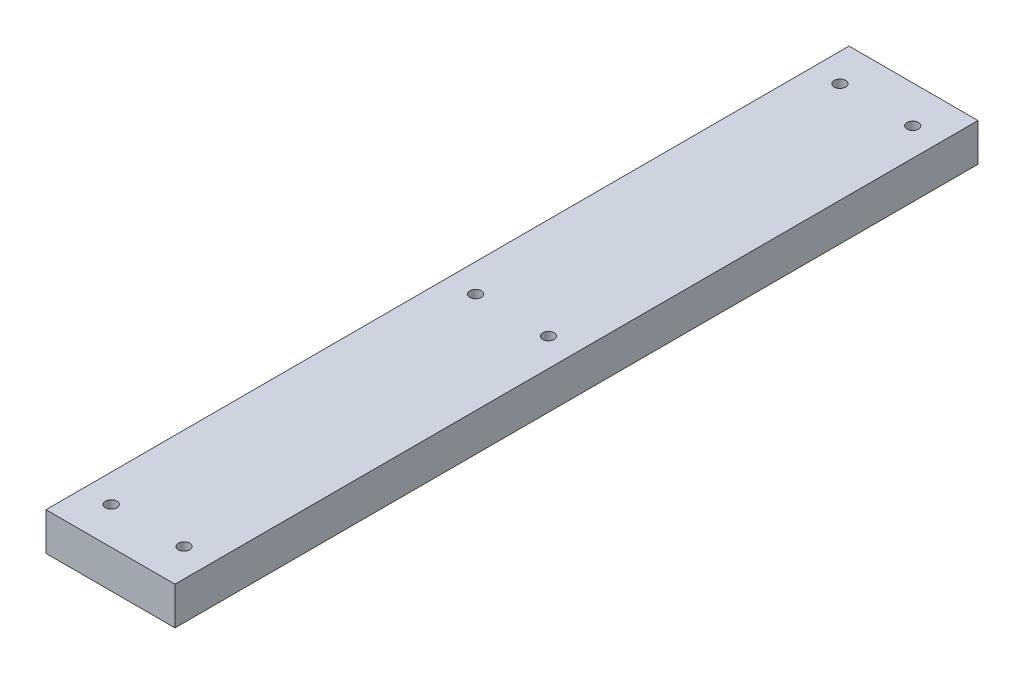
SolidWorks part; units mm, degrees
material "Acrylic (BLUE)"
ref_plane "Front Plane" through (0, 0, 0) normal (0, 0, 1) x (1, 0, 0)
ref_plane "Top Plane" through (0, 0, 0) normal (0, 1, 0) x (1, 0, 0)
ref_plane "Right Plane" through (0, 0, 0) normal (1, 0, 0) x (0, 0, -1)
sketch "Sketch1" plane through (0, 0, 0) normal (0, 1, 0) x (1, 0, 0)
  line L0 (-11.1125, 69.85) -> (11.1125, -69.85) construction
  line L1 (-11.1125, 69.85) -> (11.1125, 69.85)
  line L2 (-11.1125, 69.85) -> (-11.1125, -69.85)
  line L3 (-11.1125, -69.85) -> (11.1125, -69.85)
  line L4 (11.1125, 69.85) -> (11.1125, -69.85)
  line L5 (11.1125, -69.85) -> (10.7666, -69.6771) construction
  dimension "D1" = 139.7
  dimension "D2" = 22.225
extrude "Boss-Extrude1" add sketch "Sketch1" along normal blind 6.604
hole_wizard "#4-40 Tapped Hole1" positions "Sketch3" profile "Sketch4" tap size "#4-40" standard "ANSI Inch"
sketch "Sketch3" plane through (0, 6.604, 0) normal (0, 1, 0) x (1, 0, 0)
  line L0 (6.35, 69.85) -> (6.35, 63.5) construction
  line L1 (11.1125, 69.85) -> (-11.1125, 69.85) construction
  line L2 (6.35, 63.5) -> (6.35, 0) construction
  line L3 (6.35, 0) -> (6.35, -63.5) construction
  line L4 (6.35, -63.5) -> (6.35, -69.85) construction
  line L5 (-11.1125, -69.85) -> (11.1125, -69.85) construction
  line L7 (-6.35, 69.85) -> (-6.35, 63.5) construction
  line L8 (-6.35, 63.5) -> (-6.35, 0) construction
  line L9 (-6.35, 0) -> (-6.35, -63.5) construction
  line L10 (-6.35, -63.5) -> (-6.35, -69.85) construction
  line L12 (-6.35, 63.5) -> (-11.1125, 63.5) construction
  line L13 (-11.1125, 69.85) -> (-11.1125, -69.85) construction
  line L15 (6.35, 63.5) -> (11.1125, 63.5) construction
  line L16 (11.1125, -69.85) -> (11.1125, 69.85) construction
  point P1 (6.35, 63.5)
  point P5 (6.35, 0)
  point P7 (6.35, -63.5)
  point P14 (-6.35, 63.5)
  point P16 (-6.35, 0)
  point P18 (-6.35, -63.5)
  dimension "D1" = 12.7
  dimension "D2" = 63.5
sketch "Sketch4" plane through (6.35, 6.604, -63.5) normal (1, 0, 0) x (0, 0, 1)
  line L0 (0, 0) -> (0, 8.2738)
  line L1 (0, 8.2738) -> (1.1303, 7.5946)
  line L2 (1.1303, 7.5946) -> (1.1303, 0)
  line L5 (1.1303, 0) -> (0, 0)
  line L10 (0, 8.2738) -> (-1.1303, 7.5946) construction
  line L11 (0, -6.35) -> (0, 107.95) construction
  dimension "Tap Drill Dia." = 2.2606
  dimension "Tap Drill Depth" = 7.5946
  dimension "Drill Angle" = 118
other "Move Face1" face at (0, 3.302, 69.85) face at (6.35, 6.604, 1.1303) face at (-6.35, 6.604, 1.1303) face at (6.35, 6.604, 64.6303) face at (-6.35, 6.604, 64.6303) face at (-11.1125, 3.302, 0) face at (-6.35, 6.604, -62.3697) face at (6.35, 6.604, -62.3697) face at (0, 3.302, -69.85) face at (11.1125, 3.302, 0) parameters "D1"=0.127
